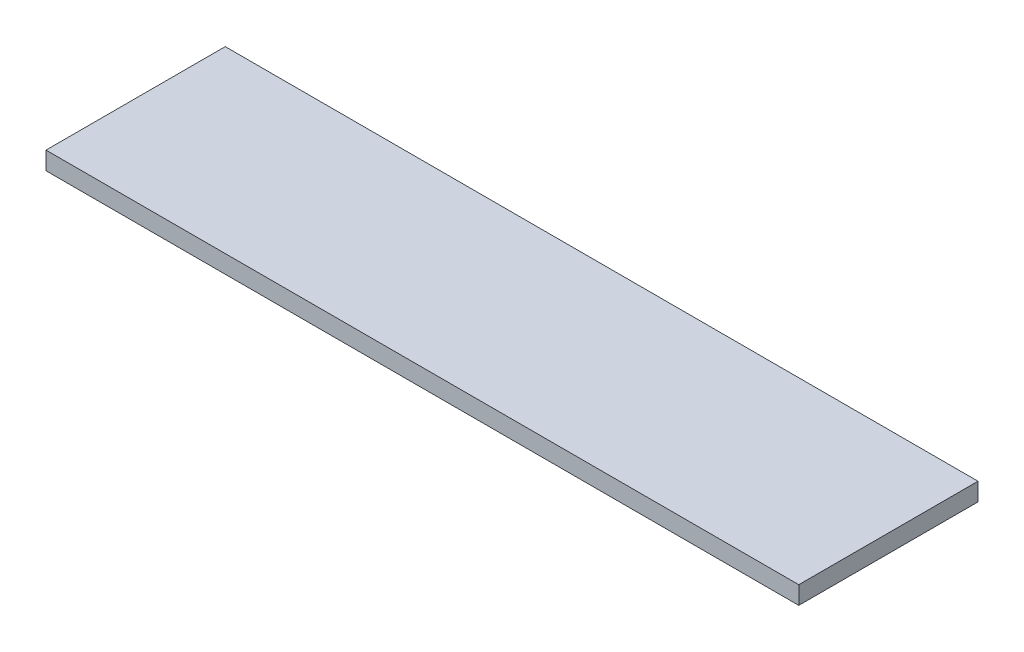
SolidWorks part; units mm, degrees
material "Простая углеродистая сталь"
ref_plane "Спереди" through (0, 0, 0) normal (0, 0, 1) x (1, 0, 0)
ref_plane "Сверху" through (0, 0, 0) normal (0, 1, 0) x (1, 0, 0)
ref_plane "Справа" through (0, 0, 0) normal (1, 0, 0) x (0, 0, -1)
sketch "Эскиз1" plane through (0, 0, 0) normal (0, 1, 0) x (1, 0, 0)
  line L1 (0, 0) -> (42, 0)
  line L2 (0, 0) -> (0, 10)
  line L3 (0, 10) -> (42, 10)
  line L4 (42, 0) -> (42, 10)
  dimension "D1" = 42
  dimension "D2" = 10
extrude "Бобышка-Вытянуть1" add sketch "Эскиз1" along normal blind 1
